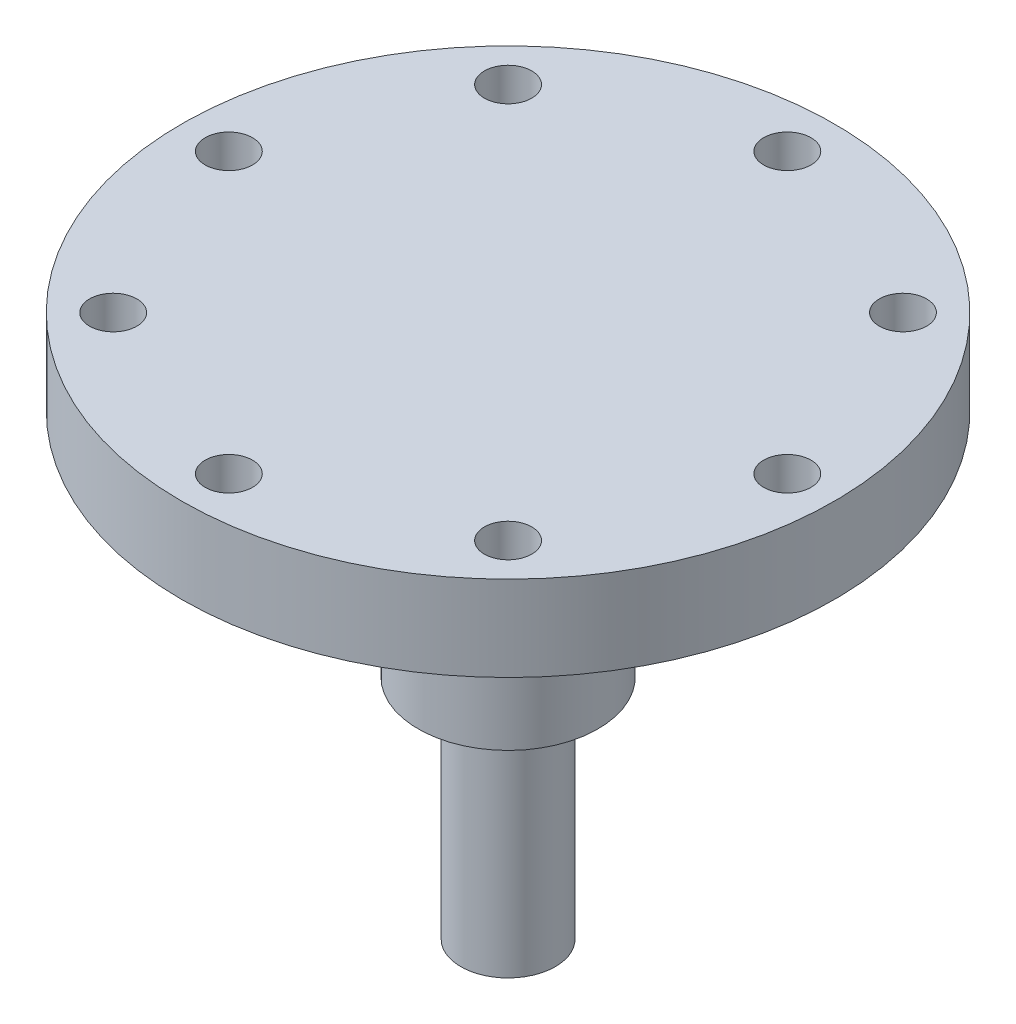
SolidWorks part; units mm, degrees
material "1023 Chapa de acero al carbono (SS)"
ref_plane "Alzado" through (0, 0, 0) normal (0, 0, 1) x (1, 0, 0)
ref_plane "Planta" through (0, 0, 0) normal (0, 1, 0) x (1, 0, 0)
ref_plane "Vista lateral" through (0, 0, 0) normal (1, 0, 0) x (0, 0, -1)
sketch "Croquis1" plane through (0, 0, 0) normal (0, 1, 0) x (1, 0, 0)
  line L0 (0, 0) -> (14.75, 0) construction
  circle A0 centre (0, 0) radius 17.25
  circle A1 centre (0, 0) radius 14.75 construction
  circle A2 centre (14.75, 0) radius 1.25
  circle A3 centre (10.4298, -10.4298) radius 1.25
  circle A4 centre (0, -14.75) radius 1.25
  circle A5 centre (-10.4298, -10.4298) radius 1.25
  circle A6 centre (-14.75, 0) radius 1.25
  circle A7 centre (-10.4298, 10.4298) radius 1.25
  circle A8 centre (0, 14.75) radius 1.25
  circle A9 centre (10.4298, 10.4298) radius 1.25
  point P22 (0, 0)
  dimension "D1" = 34.5
  dimension "D2" = 29.5
  dimension "D3" = 2.5
  dimension "D4" = 8
extrude "Saliente-Extruir1" add sketch "Croquis1" along normal blind 4.5
sketch "Croquis3" plane through (0, 0, 0) normal (0, -1, 0) x (1, 0, 0)
  circle A0 centre (0, 0) radius 4.75
  dimension "D1" = 9.5
extrude "Saliente-Extruir3" add sketch "Croquis3" along normal blind 12.175
sketch "Croquis4" plane through (0, 0, 0) normal (0, -1, 0) x (1, 0, 0)
  circle A0 centre (0, 0) radius 6
  dimension "D1" = 12
extrude "Saliente-Extruir4" add sketch "Croquis4" along normal blind 3
sketch "Croquis5" plane through (0, -12.175, 0) normal (0, -1, 0) x (1, 0, 0)
  circle A0 centre (0, 0) radius 2.5
  dimension "D1" = 5
extrude "Saliente-Extruir5" add sketch "Croquis5" along normal blind 12
